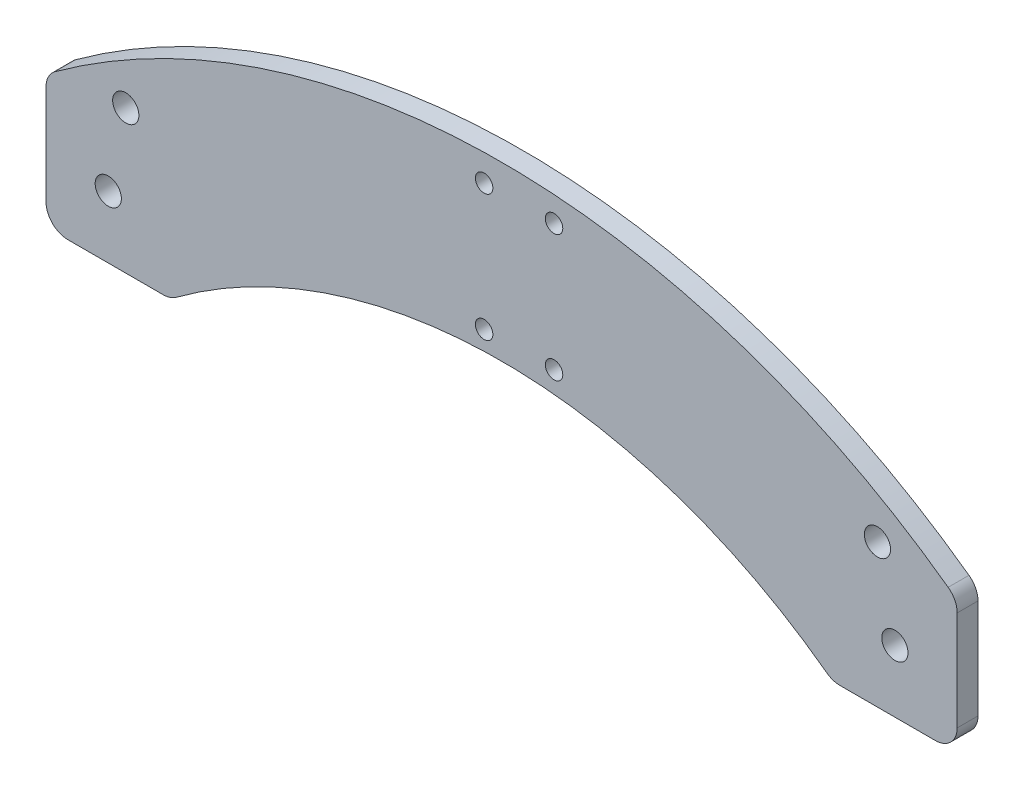
SolidWorks part; units mm, degrees
ref_plane "Front Plane" through (0, 0, 0) normal (0, 0, 1) x (1, 0, 0)
ref_plane "Top Plane" through (0, 0, 0) normal (0, 1, 0) x (1, 0, 0)
ref_plane "Right Plane" through (0, 0, 0) normal (1, 0, 0) x (0, 0, -1)
sketch "Sketch1" plane through (0, 0, 0) normal (0, 0, 1) x (1, 0, 0)
  line L0 (-14.25, -9.25) -> (-14.25, 13.5361)
  line L4 (194.25, 13.5361) -> (194.25, -9.25)
  line L5 (189.25, -14.25) -> (167.4192, -14.25)
  line L9 (12.5808, -14.25) -> (-9.25, -14.25)
  line L10 (14.25, -30) -> (14.25, 6.9138) construction
  line L11 (194.25, 14.25) -> (194.25, -14.25) construction
  line L12 (194.25, -14.25) -> (185.75, -30) construction
  line L13 (165.75, -30) -> (165.75, 6.9138) construction
  circle A0 centre (86, 44.6) radius 2
  circle A1 centre (86, 15.6) radius 2
  circle A2 centre (102, 44.6) radius 2
  circle A3 centre (102, 15.6) radius 2
  circle A4 centre (180, 0) radius 3
  circle A5 centre (0, 0) radius 3
  arc A6 (164.4415, -13.2667) -> (15.5585, -13.2667) centre (90, -113.6831) ccw
  arc A7 (-12.1864, 17.583) -> (192.1864, 17.583) centre (90, -123.25) cw
  circle A8 centre (4, 18.5) radius 3
  circle A9 centre (176, 18.5) radius 3
  arc A10 (194.25, -9.25) -> (189.25, -14.25) centre (189.25, -9.25) cw
  arc A11 (-14.25, -9.25) -> (-9.25, -14.25) centre (-9.25, -9.25) ccw
  arc A12 (167.4192, -14.25) -> (164.4415, -13.2667) centre (167.4192, -9.25) cw
  arc A13 (15.5585, -13.2667) -> (12.5808, -14.25) centre (12.5808, -9.25) cw
  arc A14 (194.25, 13.5361) -> (192.1864, 17.583) centre (189.25, 13.5361) ccw
  arc A15 (-12.1864, 17.583) -> (-14.25, 13.5361) centre (-9.25, 13.5361) ccw
  point P56 (194.25, -14.25)
  point P59 (-14.25, -14.25)
  point P62 (165.75, -14.25)
  point P65 (14.25, -14.25)
  dimension "D1" = 6
  dimension "D2" = 4
  dimension "D3" = 125
  dimension "D4" = 65
  dimension "D5" = 6
  dimension "D6" = 174
  dimension "D7" = 5
  dimension "D8" = 5
  dimension "D9" = 5
  dimension "D10" = 5
extrude "Boss-Extrude1" add sketch "Sketch1" along normal blind 4.7625
sketch "Sketch3" plane through (0, 0, 4.7625) normal (0, 0, 1) x (1, 0, 0)
  line L0 (12.3006, 19.0354) -> (8.0644, -0.5571)
  line L1 (80, 39.0583) -> (80, 25.7453)
  line L2 (108, 38.1191) -> (108, 25.1039)
  line L3 (167.7323, 18.8829) -> (171.9356, -0.5571)
  line L4 (13.9227, 26.5373) -> (80, 16.9347) construction
  line L5 (166.0773, 26.5373) -> (108, 16.0744) construction
  line L6 (151.778, 27.0095) -> (113.8865, 20.1832)
  line L7 (130.0058, 16.9905) -> (161.9588, 22.747)
  line L8 (52.7151, 17.8683) -> (17.9068, 22.9268)
  line L9 (29.2141, 27.3466) -> (74.2809, 20.7973)
  arc A0 (161.9588, 22.747) -> (167.7323, 18.8829) centre (162.8453, 17.8262) cw
  arc A1 (108, 38.1191) -> (113.7055, 43.0691) centre (113, 38.1191) cw
  arc A2 (168.0147, -8.4467) -> (11.9853, -8.4467) centre (90, -113.6831) ccw
  arc A3 (164.2159, -5.734) -> (129.6301, 11.1786) centre (90, -113.6831) ccw
  circle A4 centre (4, 18.5) radius 3 construction
  arc A5 (188.6627, 12.7267) -> (-8.6627, 12.7267) centre (90, -123.25) ccw
  arc A6 (152.3597, 32.7477) -> (113.7055, 43.0691) centre (90, -123.25) ccw
  circle A7 centre (0, 0) radius 3 construction
  circle A8 centre (180, 0) radius 3 construction
  circle A9 centre (176, 18.5) radius 3 construction
  circle A10 centre (102, 44.6) radius 2 construction
  circle A11 centre (86, 44.6) radius 2 construction
  arc A12 (74.5399, 44.0371) -> (28.5482, 33.1075) centre (90, -123.25) ccw
  arc A13 (53.1281, 12.0208) -> (15.7841, -5.734) centre (90, -113.6831) ccw
  arc A14 (108, 25.1039) -> (113.8865, 20.1832) centre (113, 25.1039) ccw
  arc A15 (80, 39.0583) -> (74.5399, 44.0371) centre (75, 39.0583) ccw
  arc A16 (80, 25.7453) -> (74.2809, 20.7973) centre (75, 25.7453) cw
  arc A17 (17.9068, 22.9268) -> (12.3006, 19.0354) centre (17.1877, 17.9788) ccw
  arc A18 (151.778, 27.0095) -> (152.3597, 32.7477) centre (151.2461, 29.962) ccw
  arc A19 (130.0058, 16.9905) -> (129.6301, 11.1786) centre (130.5377, 14.0381) ccw
  arc A20 (52.7151, 17.8683) -> (53.1281, 12.0208) centre (52.2837, 14.8995) cw
  arc A21 (29.2141, 27.3466) -> (28.5482, 33.1075) centre (29.6455, 30.3154) cw
  arc A22 (164.2159, -5.734) -> (171.9356, -0.5571) centre (167.0485, -1.6138) ccw
  arc A23 (15.7841, -5.734) -> (8.0644, -0.5571) centre (12.9515, -1.6138) cw
  point P46 (80, 44.4521)
  dimension "D6" = 8
  dimension "D8" = 6
  dimension "D13" = 5
  dimension "D14" = 3
  dimension "D15" = 5
  dimension "D3" = 8
  dimension "D4" = 8
  dimension "D5" = 8
  dimension "D7" = 6
  dimension "D9" = 3
  dimension "D10" = 6
  dimension "D11" = 3
  dimension "D12" = 6
  dimension "D1" = 6
  dimension "D2" = 6
extrude "Cut-Extrude1" [suppressed] cut sketch "Sketch3" against normal offset from surface (4.35 mm away) 2
